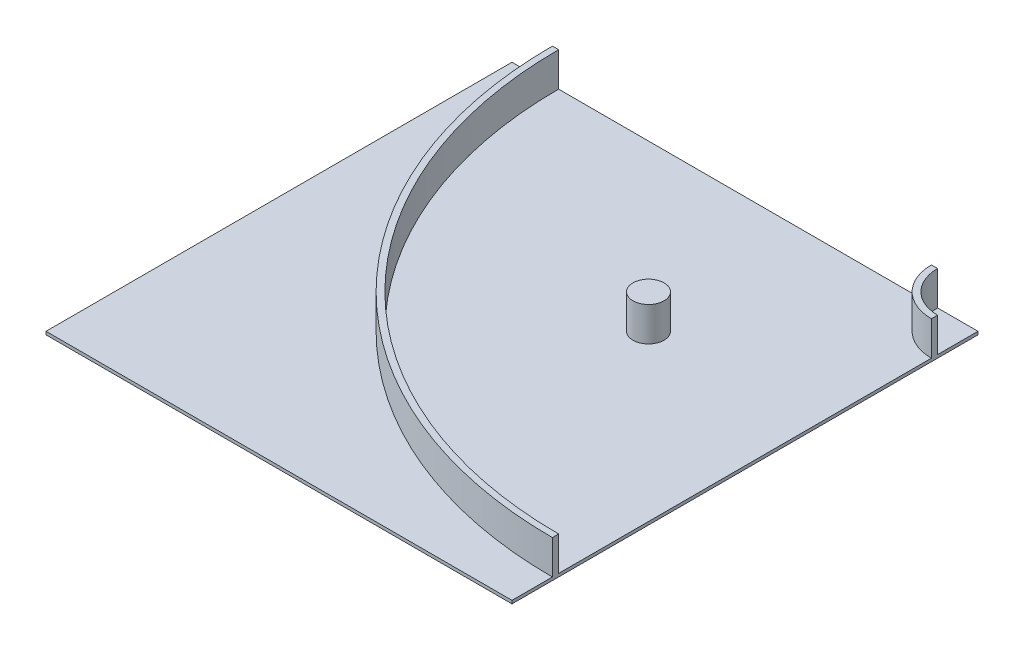
SolidWorks part; units mm, degrees
ref_plane "Front Plane" through (0, 0, 0) normal (0, 0, 1) x (1, 0, 0)
ref_plane "Top Plane" through (0, 0, 0) normal (0, 1, 0) x (1, 0, 0)
ref_plane "Right Plane" through (0, 0, 0) normal (1, 0, 0) x (0, 0, -1)
sketch "Sketch2" plane through (0, 0, 0) normal (0, 1, 0) x (1, 0, 0)
  line L1 (-750, 750) -> (750, 750)
  line L2 (-750, 750) -> (-750, -750)
  line L3 (-750, -750) -> (750, -750)
  line L4 (750, 750) -> (750, -750)
  line L5 (-750, 750) -> (750, -750) construction
  line L6 (-750, -750) -> (750, 750) construction
  point P0 (0, 0)
  dimension "D1" = 1500
  dimension "D2" = 1500
extrude "Boss-Extrude1" add sketch "Sketch2" along normal blind 10
sketch "Sketch3" plane through (0, 10, 0) normal (0, 1, 0) x (1, 0, 0)
  line L0 (620, 750) -> (620, -750) construction
  line L1 (750, 750) -> (-750, 750) construction
  line L2 (-750, -750) -> (750, -750) construction
  line L3 (600, 750) -> (600, -750) construction
  line L4 (750, -750) -> (750, 750) construction
  line L5 (-750, -600) -> (750, -600) construction
  line L6 (-750, 750) -> (-750, -750) construction
  line L7 (-750, -620) -> (750, -620) construction
  line L8 (-750, 0) -> (750, 0) construction
  line L9 (0, 750) -> (0, -750) construction
  line L10 (-750, 620) -> (750, 620) construction
  line L11 (-750, 600) -> (750, 600) construction
  line L12 (-620, 750) -> (-620, -750) construction
  line L13 (-600, 750) -> (-600, -750) construction
  circle A0 centre (750, 750) radius 150
  circle A1 centre (750, 750) radius 1350
  circle A2 centre (750, 750) radius 130
  circle A3 centre (750, 750) radius 1370
  line M3 (750, -750) -> (750, 750)
  line M4 (750, 750) -> (-750, 750)
  dimension "D6" = 150
  dimension "D5" = 20
  dimension "D7" = 20
  dimension "D8" = 150
extrude "Boss-Extrude2" add sketch "Sketch3" along normal blind 110 contours A3 A1 M4 M3 | A2 A0 M4 M3
sketch "Sketch4" plane through (0, 10, 0) normal (0, 1, 0) x (1, 0, 0)
  line L0 (750, 750) -> (-750, -750) construction
  line L1 (643.934, 643.934) -> (-204.5942, -204.5942)
  arc A0 (-600, 750) -> (750, -600) centre (750, 750) ccw construction
  circle A1 centre (219.6699, 219.6699) radius 50
  arc A2 (600, 750) -> (750, 600) centre (750, 750) ccw construction
  dimension "D1" = 100
extrude "Boss-Extrude3" add sketch "Sketch4" along normal up to surface (110 mm away) contours L1 A1 | L1 A1 up to face at (-70.8326, 120, 70.8326)
equation "\"CellSize\"=1500"
equation "\"D1@Sketch2\"=\"CellSize\""
equation "\"D2@Sketch2\"=\"CellSize\""
equation "\"TrackWidth\"= 1200"
equation "\"C\"=342.079"
equation "\"WallWidth\"=20"
equation "\"D6@Sketch3\"=\"EdgeWidth\""
equation "\"D5@Sketch3\"=\"WallWidth\""
equation "\"D7@Sketch3\"=\"WallWidth\""
equation "\"EdgeWidth\"= ( \"CellSize\" - \"TrackWidth\" ) / 2"
equation "\"D8@Sketch3\"=\"EdgeWidth\""
